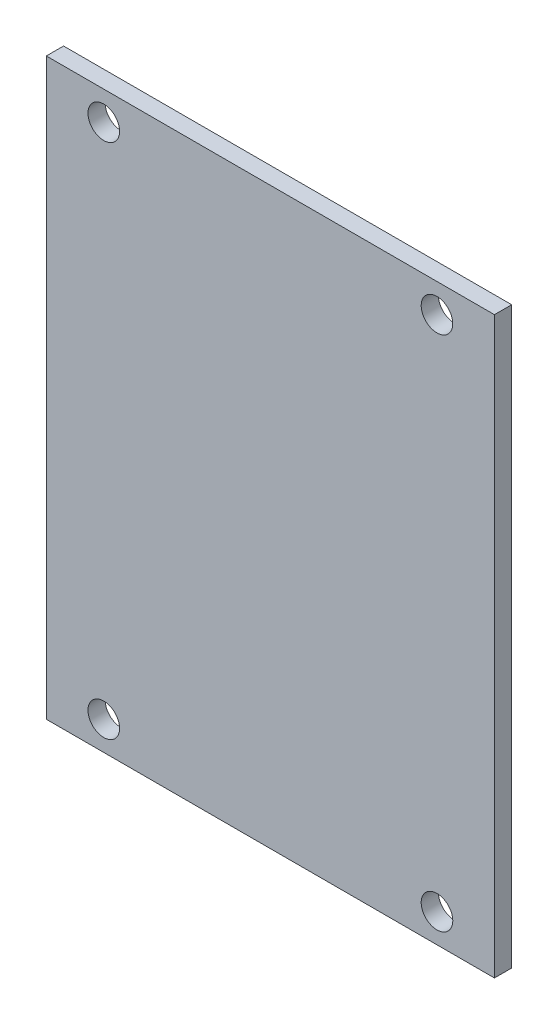
SolidWorks part; units mm, degrees
ref_plane "前视基准面" through (0, 0, 0) normal (0, 0, 1) x (1, 0, 0)
ref_plane "上视基准面" through (0, 0, 0) normal (0, 1, 0) x (1, 0, 0)
ref_plane "右视基准面" through (0, 0, 0) normal (1, 0, 0) x (0, 0, -1)
sketch "草图1" plane through (0, 0, 0) normal (0, 0, 1) x (1, 0, 0)
  line L1 (0, 0) -> (78, 0)
  line L2 (0, 0) -> (0, 100)
  line L3 (0, 100) -> (78, 100)
  line L4 (78, 0) -> (78, 100)
  dimension "D1" = 78
  dimension "D2" = 100
extrude "凸台-拉伸1" add sketch "草图1" along normal blind 3
sketch "草图3" plane through (0, 0, 3) normal (0, 0, 1) x (1, 0, 0)
  line L0 (78, 50) -> (0, 50) construction
  line L1 (78, 0) -> (78, 100) construction
  line L2 (0, 100) -> (0, 0) construction
  line L3 (0, 50) -> (39, 50) construction
  line L4 (39, 50) -> (39, 23.0739) construction
  circle A0 centre (10, 95) radius 2.75
  circle A1 centre (10, 5) radius 2.75
  circle A2 centre (68, 5) radius 2.75
  circle A3 centre (68, 95) radius 2.75
  dimension "D1" = 5.5
  dimension "D2" = 58
  dimension "D3" = 90
extrude "切除-拉伸1" cut sketch "草图3" against normal blind 10
